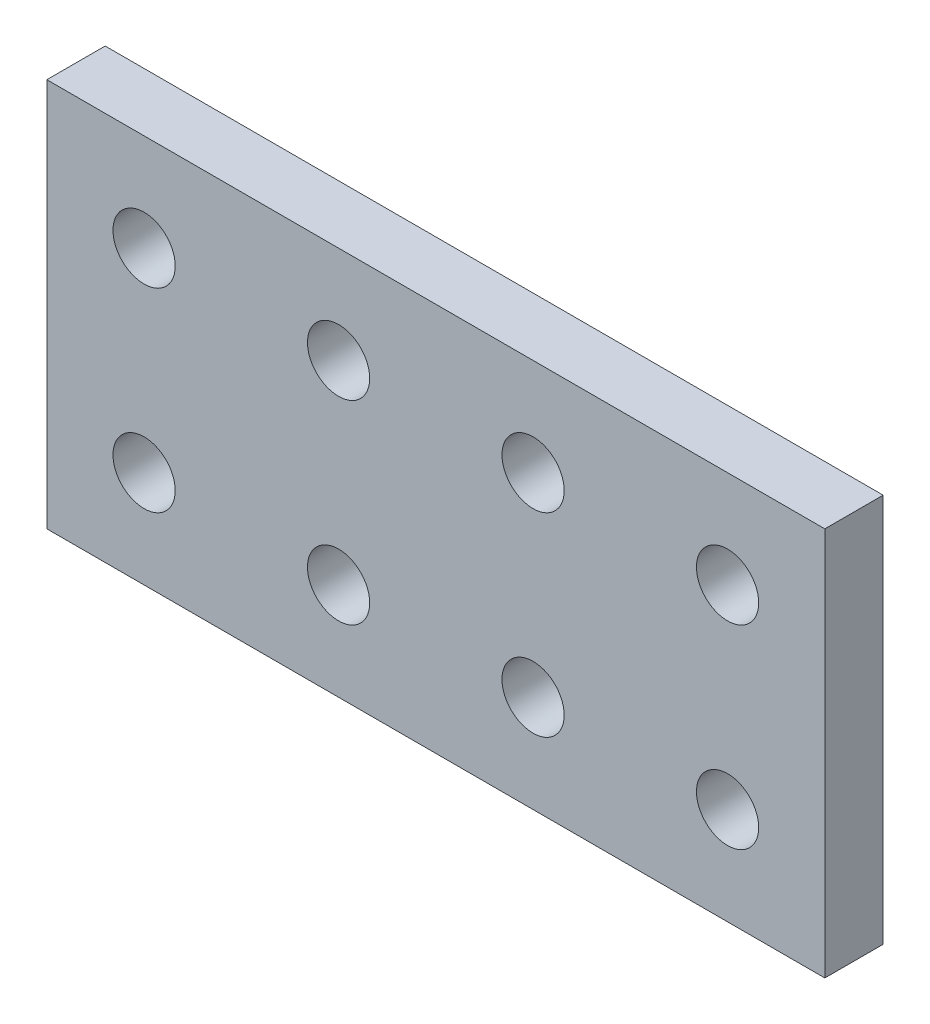
SolidWorks part; units mm, degrees
material "Thornel Mat VMA"
ref_plane "前视基准面" through (0, 0, 0) normal (0, 0, 1) x (1, 0, 0)
ref_plane "上视基准面" through (0, 0, 0) normal (0, 1, 0) x (1, 0, 0)
ref_plane "右视基准面" through (0, 0, 0) normal (1, 0, 0) x (0, 0, -1)
other "Configuration Table"
sketch "草图1" plane through (0, 0, 0) normal (0, 0, 1) x (1, 0, 0)
  line L0 (28.1488, 17.927) -> (58.1488, 17.927) construction
  line L1 (28.1488, 22.927) -> (58.1488, 22.927) construction
  line L2 (28.1488, 22.927) -> (28.1488, 12.927) construction
  line L3 (28.1488, 12.927) -> (58.1488, 12.927) construction
  line L4 (58.1488, 22.927) -> (58.1488, 12.927) construction
  line L5 (43.1488, 22.927) -> (43.1488, 12.927) construction
  line L6 (43.1488, 27.927) -> (43.1488, 22.927) construction
  line L7 (23.1488, 27.927) -> (63.1488, 27.927)
  line L8 (23.1488, 27.927) -> (23.1488, 7.927)
  line L9 (23.1488, 7.927) -> (63.1488, 7.927)
  line L10 (63.1488, 27.927) -> (63.1488, 7.927)
  circle A0 centre (48.1488, 22.927) radius 1.6
  circle A1 centre (58.1488, 22.927) radius 1.6
  circle A2 centre (38.1488, 22.927) radius 1.6
  circle A3 centre (28.1488, 22.927) radius 1.6
  circle A4 centre (28.1488, 12.927) radius 1.6
  circle A5 centre (38.1488, 12.927) radius 1.6
  circle A6 centre (48.1488, 12.927) radius 1.6
  circle A7 centre (58.1488, 12.927) radius 1.6
  dimension "D3" = 40
  dimension "D7" = 3.2
  dimension "D1" = 10
  dimension "D2" = 30
  dimension "D4" = 10
  dimension "D5" = 20
  dimension "D6" = 10
  dimension "D8" = 5
extrude "凸台-拉伸1" add sketch "草图1" along normal blind 3
